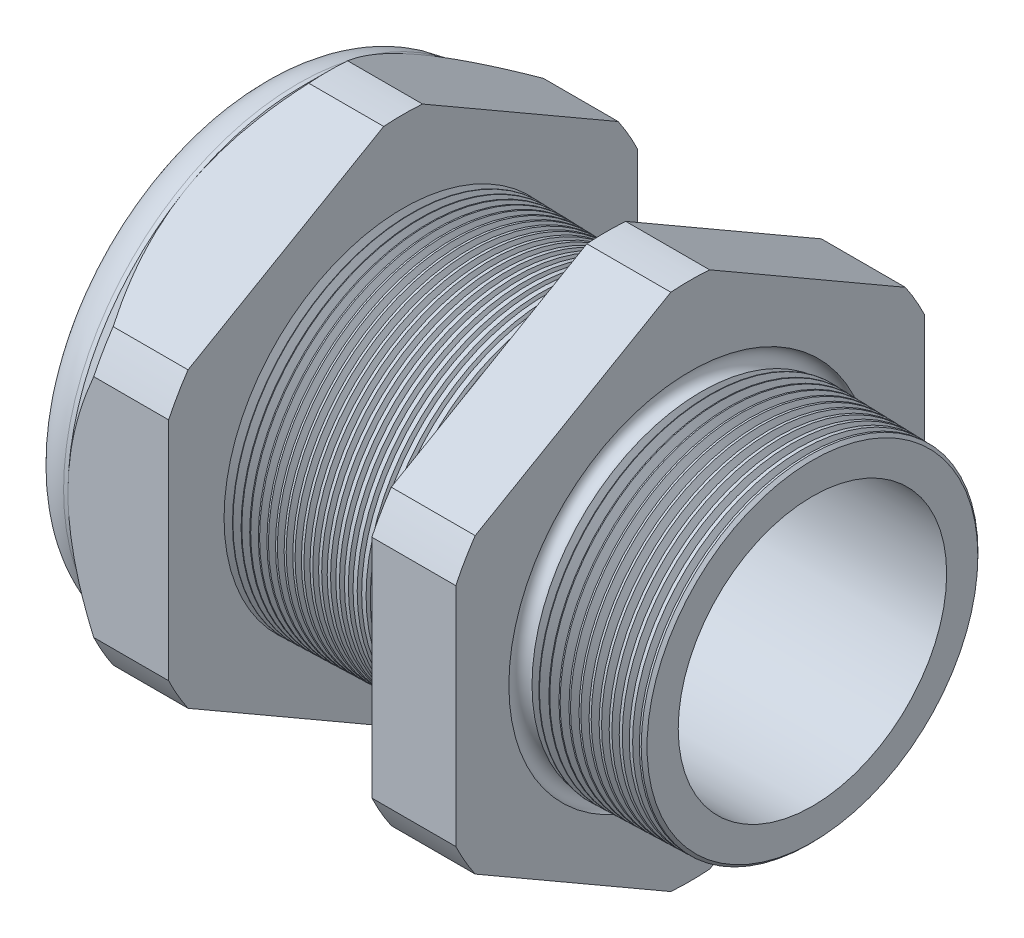
SolidWorks part; units mm, degrees
ref_plane "Front Plane" through (0, 0, 0) normal (0, 0, 1) x (1, 0, 0)
ref_plane "Top Plane" through (0, 0, 0) normal (0, 1, 0) x (1, 0, 0)
ref_plane "Right Plane" through (0, 0, 0) normal (1, 0, 0) x (0, 0, -1)
sketch "Sketch10" plane through (0, 0, 0) normal (0, 0, 1) x (1, 0, 0)
  line L0 (0, 0) -> (-115.3565, 0) construction
  line L1 (-46.736, 12.446) -> (-33.536, 12.446)
  line L2 (3.048, 11.996) -> (3.048, 15.044)
  line L3 (-7.874, 15.33) -> (3.048, 15.044)
  line L4 (-7.874, 41.91) -> (-7.874, 15.33)
  line L5 (-7.874, 41.91) -> (-15.374, 41.91)
  line L6 (-15.374, 41.91) -> (-15.374, 15.5264)
  line L7 (-33.536, 16.002) -> (-15.374, 15.5264)
  line L8 (-33.536, 16.002) -> (-33.536, 41.91)
  line L9 (-33.536, 41.91) -> (-42.536, 41.91)
  line L10 (-42.536, 41.91) -> (-42.536, 20.955)
  line L11 (-42.536, 20.955) -> (-46.736, 20.955)
  line L12 (-46.736, 20.955) -> (-46.736, 12.446)
  line L13 (-33.536, 12.446) -> (3.048, 11.996)
  dimension "D1" = 49.784
  dimension "D2" = 24.892
  dimension "D3" = 1.5
  dimension "D4" = 3.048
  dimension "A" = 32.004
  dimension "D6" = 41.91
  dimension "D8" = 83.82
  dimension "D9" = 4.2
  dimension "D10" = 9
  dimension "D11" = 7.5
  dimension "D" = 10.922
revolve "Revolve2" add sketch "Sketch10" angle 360 about L0
sketch "Sketch12" plane through (-42.536, 0, 0) normal (-1, 0, 0) x (0, 0, 1)
  line L1 (-1.7346, 23.1953) -> (-19.2204, 13.0998)
  line L2 (-20.955, 10.0954) -> (-20.955, -10.0954)
  line L3 (-19.2204, -13.0998) -> (-1.7346, -23.1953)
  line L4 (1.7346, -23.1953) -> (19.2204, -13.0998)
  line L5 (20.955, -10.0954) -> (20.955, 10.0954)
  line L6 (19.2204, 13.0998) -> (1.7346, 23.1953)
  circle A0 centre (0, 0) radius 20.955 construction
  arc A1 (1.7346, 23.1953) -> (-1.7346, 23.1953) centre (0, 0) ccw
  arc A2 (-19.2204, 13.0998) -> (-20.955, 10.0954) centre (0, 0) ccw
  arc A3 (-20.955, -10.0954) -> (-19.2204, -13.0998) centre (0, 0) ccw
  arc A4 (-1.7346, -23.1953) -> (1.7346, -23.1953) centre (0, 0) ccw
  arc A5 (19.2204, -13.0998) -> (20.955, -10.0954) centre (0, 0) ccw
  arc A6 (20.955, 10.0954) -> (19.2204, 13.0998) centre (0, 0) ccw
  dimension "D2" = 46.5201
  dimension "D1" = 41.91
extrude "Cut-Extrude2" cut sketch "Sketch12" against normal through all flip side to cut
fillet "Fillet4" radius 3.81 1 edges at (-46.736, 0, -20.955)
sketch "Sketch19" plane through (-42.536, 0, 0) normal (-1, 0, 0) x (0, 0, 1)
  line L0 (20.955, 0) -> (20.955, 10.0954) construction
  circle A0 centre (0, 0) radius 20.955
extrude "Cut-Extrude3" cut sketch "Sketch19" against normal blind 3.998 draft 45 flip side to cut
chamfer "Chamfer1" distance 0.254 angle 45 1 edges at (3.048, 0, -15.044)
sketch "Sketch21" plane through (-46.736, 0, 0) normal (-1, 0, 0) x (0, 0, 1)
  circle A0 centre (0, 0) radius 12.446
  circle A2 centre (0, 0) radius 12.446 construction
extrude "plug" add sketch "Sketch21" against normal blind 12.7 separate body
sketch "Sketch22" plane through (-46.736, 0, 0) normal (-1, 0, 0) x (0, 0, 1)
  circle A0 centre (0, 0) radius 12.192
  circle A1 centre (0, 0) radius 12.446 construction
  dimension "D1" = 0.254
extrude "Cut-Extrude4" cut sketch "Sketch22" against normal blind 0.508
sketch "Sketch27" plane through (-46.228, 0, 0) normal (-1, 0, 0) x (0, 0, 1)
  line L0 (-4.3624, 0) -> (4.3624, 0) construction
  circle A0 centre (-8.8768, 0) radius 3.302
  circle A1 centre (0, 0) radius 12.192 construction
  dimension "D1" = 0.0132
  dimension "holedia" = 6.604
extrude "plugholes" cut sketch "Sketch27" against normal through all
pattern_circular "CirPattern1" count 6 over 360 about axis through (0, 0, 0) along (1, 0, 0) of "plugholes"
sketch "Sketch28" [suppressed] plane through (-38.354, 0, 0) normal (-1, 0, 0) x (0, 0, 1)
  circle A0 centre (0, 0) radius 1.905
  dimension "midholedia" = 6.604
extrude "midhole" [suppressed] cut sketch "Sketch28" against normal through all
sketch "Sketch29" plane through (0, 0, 0) normal (0, 0, 1) x (1, 0, 0)
  line L0 (-33.536, 16.002) -> (-32.803, 15.9828)
  line L1 (-15.374, 15.5264) -> (-33.536, 16.002) construction
  line L2 (-32.803, 15.9828) -> (-33.1861, 15.3576)
  line L3 (-33.1861, 15.3576) -> (-33.536, 16.002)
  dimension "D1" = 60
  dimension "D2" = 60
  dimension "D3" = 0.635
revolve "Cut-Revolve1" cut sketch "Sketch29" angle 360 about axis through (0, 0, 0) along (-1, 0, 0)
pattern_linear "LPattern1" count 24 spacing 0.762 along (1, 0, 0) of "Cut-Revolve1"
sketch "Sketch30" plane through (0, 0, 0) normal (0, 0, 1) x (1, 0, 0)
  line L0 (-7.874, 15.33) -> (-6.9944, 15.307)
  line L1 (-7.874, 23.1953) -> (-7.874, 13.0998) construction
  line L2 (2.7941, 15.0507) -> (-7.874, 15.33) construction
  line L3 (-6.9944, 15.307) -> (-7.4542, 14.5568)
  line L4 (-7.4542, 14.5568) -> (-7.874, 15.33)
  dimension "D1" = 60
  dimension "D2" = 60
  dimension "D3" = 0.762
revolve "Cut-Revolve2" cut sketch "Sketch30" angle 360 about axis through (0, 0, 0) along (-1, 0, 0)
pattern_linear "LPattern2" count 12 spacing 0.889 along (1, 0, 0) of "Cut-Revolve2"
sketch "Sketch31" [suppressed] plane through (-38.354, 0, 0) normal (-1, 0, 0) x (0, 0, 1)
  line L0 (-1.905, 1.905) -> (1.905, 1.905)
  line L1 (-1.905, -1.905) -> (1.905, -1.905)
  circle A0 centre (0, 0) radius 1.905 construction
  arc A1 (-1.905, 1.905) -> (-1.905, -1.905) centre (-1.905, 0) ccw
  arc A2 (1.905, 1.905) -> (1.905, -1.905) centre (1.905, 0) cw
extrude "Cut-Extrude5" [suppressed] cut sketch "Sketch31" against normal through all
sketch "Sketch32" plane through (0, 0, 0) normal (0, 0, 1) x (1, 0, 0)
  line L0 (-7.874, 23.1953) -> (-7.874, 13.0998) construction
  circle A0 centre (-7.747, 15.33) radius 0.889
  dimension "D2" = 1.778
  dimension "D1" = 0.127
revolve "Cut-Revolve3" cut sketch "Sketch32" angle 360 about axis through (0, 0, 0) along (-1, 0, 0)
